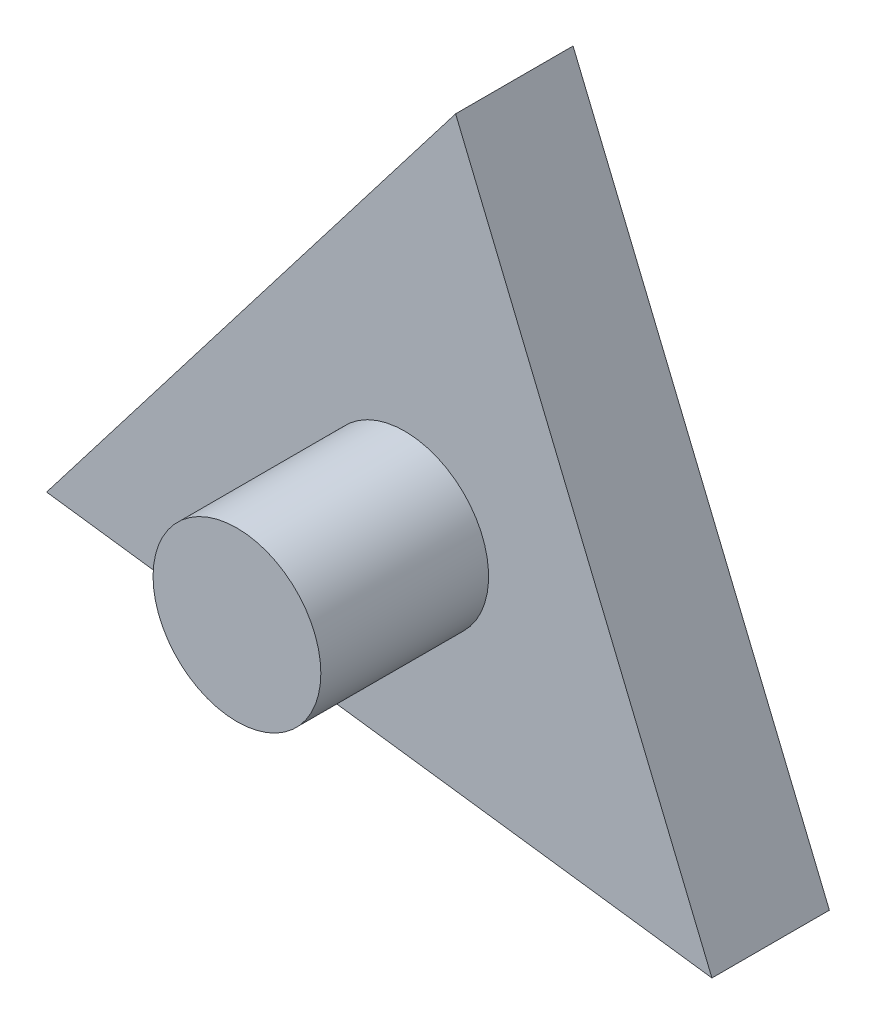
SolidWorks part; units mm, degrees
ref_plane "Plan de face" through (0, 0, 0) normal (0, 0, 1) x (1, 0, 0)
ref_plane "Plan de dessus" through (0, 0, 0) normal (0, 1, 0) x (1, 0, 0)
ref_plane "Plan de droite" through (0, 0, 0) normal (1, 0, 0) x (0, 0, -1)
sketch "Esquisse1" plane through (0, 0, 0) normal (0, 0, 1) x (1, 0, 0)
  line L0 (-21.3435, -8.8199) -> (3.0335, 22.8939)
  line L1 (3.0335, 22.8939) -> (18.31, -14.0741)
  line L2 (18.31, -14.0741) -> (-21.3435, -8.8199)
  line L3 (-21.3435, -8.8199) -> (10.6717, 4.4099) construction
  line L4 (3.0335, 22.8939) -> (-1.5168, -11.447) construction
  point P5 (0, 27.2373)
  dimension "D1" = 40
extrude "Boss.-Extru.1" add sketch "Esquisse1" along normal blind 7
sketch "Esquisse2" plane through (0, 0, 7) normal (0, 0, 1) x (1, 0, 0)
  circle A0 centre (0, 0) radius 5
  dimension "D1" = 10
extrude "Boss.-Extru.2" add sketch "Esquisse2" along normal blind 10
